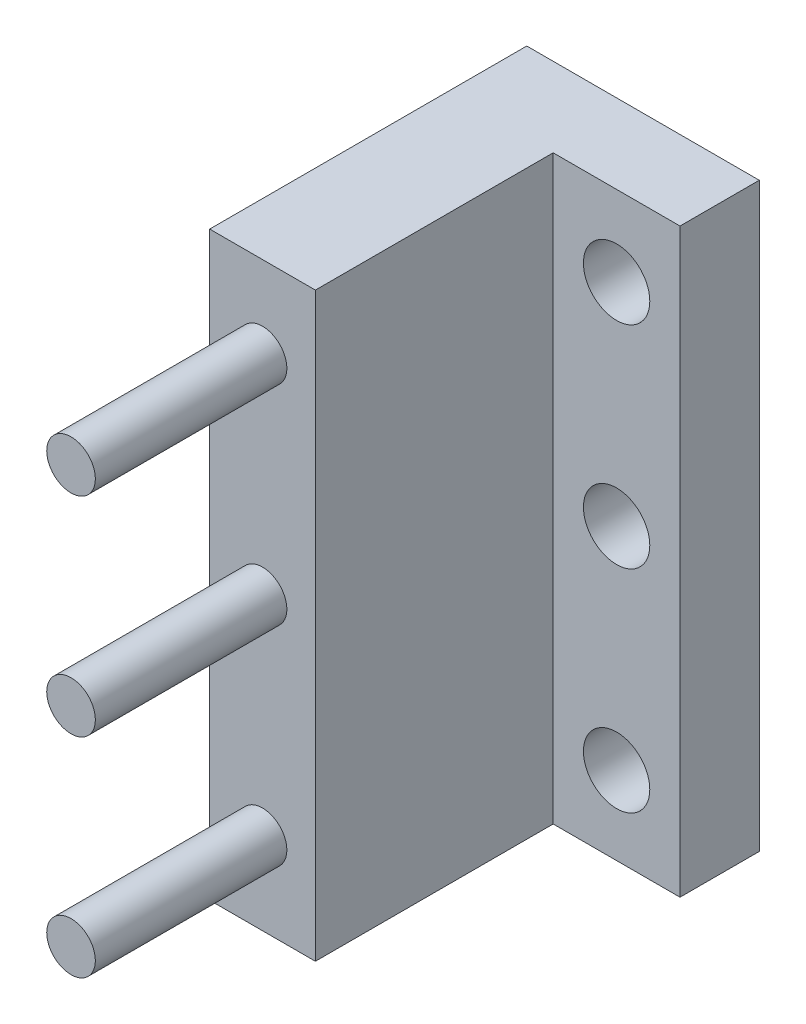
SolidWorks part; units mm, degrees
material "Cast Alloy Steel"
ref_plane "Front Plane" through (0, 0, 0) normal (0, 0, 1) x (1, 0, 0)
ref_plane "Top Plane" through (0, 0, 0) normal (0, 1, 0) x (1, 0, 0)
ref_plane "Right Plane" through (0, 0, 0) normal (1, 0, 0) x (0, 0, -1)
sketch "Sketch1" plane through (0, 0, 25.4) normal (0, 0, 1) x (1, 0, 0)
  line L2 (-187.96, 125.4701) -> (-173.99, 125.4701)
  line L3 (-187.96, 125.4701) -> (-187.96, 90.5451)
  line L4 (-187.96, 90.5451) -> (-173.99, 90.5451)
  line L5 (-173.99, 125.4701) -> (-173.99, 90.5451)
  line L6 (-190.5, 692.1441) -> (-190.5, 31.7441) construction
  line L7 (-165.1, 31.7441) -> (-190.5, 31.7441) construction
  point P0 (-175.0493, 87.7507)
  dimension "D1" = 34.925
  dimension "D2" = 13.97
  dimension "D3" = 2.54
  dimension "D4" = 58.801
extrude "Boss-Extrude1" add sketch "Sketch1" along normal blind 4.7625
sketch "Sketch2" plane through (0, 0, 30.1625) normal (0, 0, 1) x (1, 0, 0)
  line L0 (-173.99, 125.4701) -> (-187.96, 125.4701) construction
  line L1 (-187.96, 90.5451) -> (-181.61, 90.5451)
  line L2 (-187.96, 90.5451) -> (-187.96, 125.4701)
  line L3 (-187.96, 125.4701) -> (-181.61, 125.4701)
  line L4 (-181.61, 90.5451) -> (-181.61, 125.4701)
  dimension "D1" = 6.35
extrude "Boss-Extrude2" add sketch "Sketch2" along normal blind 14.2875
sketch "Sketch3" plane through (0, 0, 44.45) normal (0, 0, 1) x (1, 0, 0)
  line L0 (-181.61, 90.5451) -> (-181.61, 125.4701) construction
  line L1 (-187.96, 90.5451) -> (-181.61, 90.5451) construction
  line L2 (-181.61, 125.4701) -> (-187.96, 125.4701) construction
  line L3 (-184.785, 120.5411) -> (-184.785, 95.474) construction
  circle A0 centre (-184.785, 120.5411) radius 1.4605
  circle A1 centre (-184.785, 108.0076) radius 1.4605
  circle A2 centre (-184.785, 95.474) radius 1.4605
  point P6 (-185.908, 105.5915)
  dimension "D1" = 2.921
  dimension "D2" = 3.175
  dimension "D3" = 4.9289
  dimension "D4" = 4.9289
extrude "Boss-Extrude3" add sketch "Sketch3" along normal blind 11.5062
sketch "Sketch4" plane through (0, 0, 30.1625) normal (0, 0, 1) x (1, 0, 0)
  circle A0 centre (-177.8, 95.2441) radius 1.9939 construction
  circle A1 centre (-177.8, 107.9441) radius 1.9939 construction
  circle A2 centre (-177.8, 120.6441) radius 1.9939 construction
  circle A3 centre (-177.8, 95.2441) radius 1.9939
  circle A4 centre (-177.8, 107.9441) radius 1.9939
  circle A5 centre (-177.8, 120.6441) radius 1.9939
extrude "Cut-Extrude1" cut sketch "Sketch4" against normal blind 11.5062
